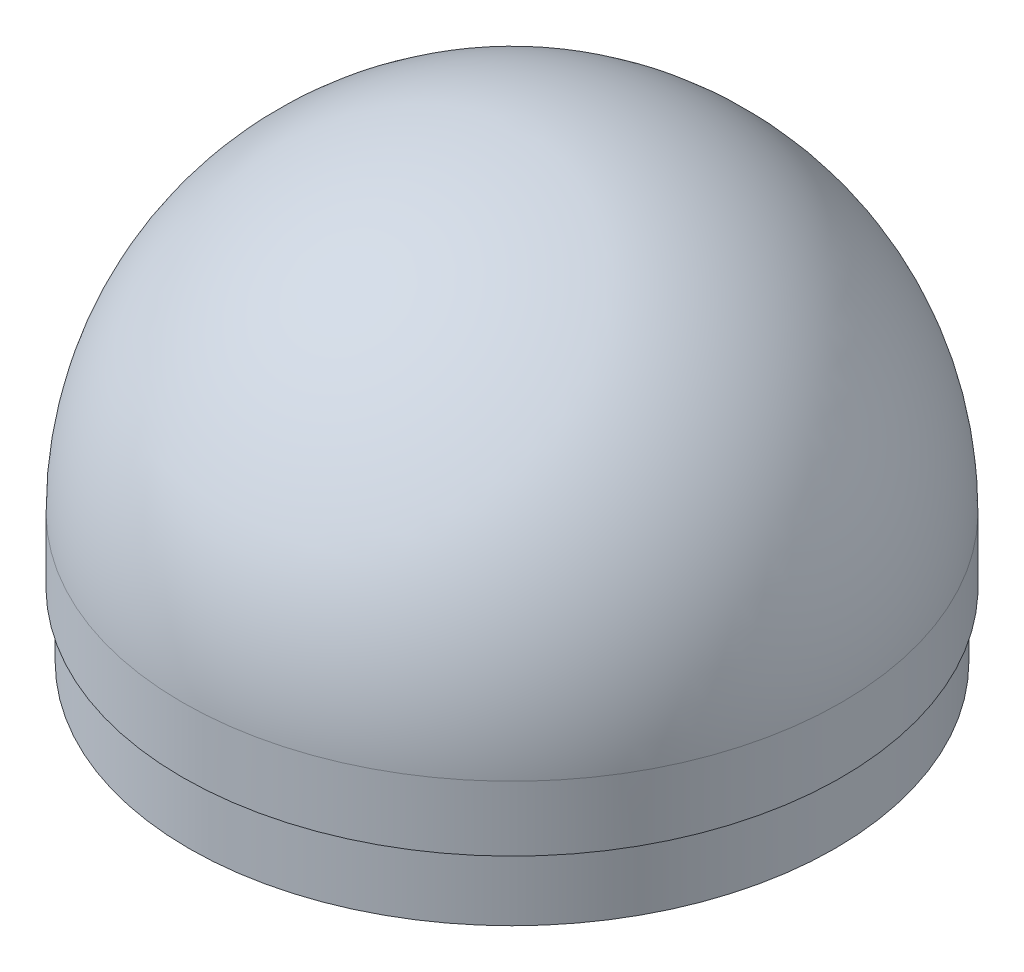
SolidWorks part; units mm, degrees
material "1060 Alloy"
ref_plane "Front Plane" through (0, 0, 0) normal (0, 0, 1) x (1, 0, 0)
ref_plane "Top Plane" through (0, 0, 0) normal (0, 1, 0) x (1, 0, 0)
ref_plane "Right Plane" through (0, 0, 0) normal (1, 0, 0) x (0, 0, -1)
sketch "Sketch1" plane through (0, 0, 0) normal (0, 0, 1) x (1, 0, 0)
  line L0 (0, 1000) -> (0, 0) construction
  line L1 (-127, 1000) -> (127, 1000) construction
  line L2 (0, 1127) -> (0, 1122)
  line L3 (122, 1000) -> (122, 950)
  line L4 (127, 1000) -> (127, 975)
  line L5 (127, 975) -> (124.5, 975)
  line L6 (124.5, 975) -> (124.5, 950)
  line L7 (124.5, 950) -> (122, 950)
  arc A0 (127, 1000) -> (0, 1127) centre (0, 1000) ccw
  arc A1 (122, 1000) -> (0, 1122) centre (0, 1000) ccw
  arc A2 (127, 1000) -> (-127, 1000) centre (0, 1000) ccw construction
  arc A3 (122, 1000) -> (-122, 1000) centre (0, 1000) ccw construction
  dimension "D1" = 1000
  dimension "D2" = 127
  dimension "D3" = 5
  dimension "D4" = 5
  dimension "D5" = 50
  dimension "D6" = 25
  dimension "D7" = 25
  dimension "D8" = 2.5
revolve "Revolve1" add sketch "Sketch1" angle 360 about L0
